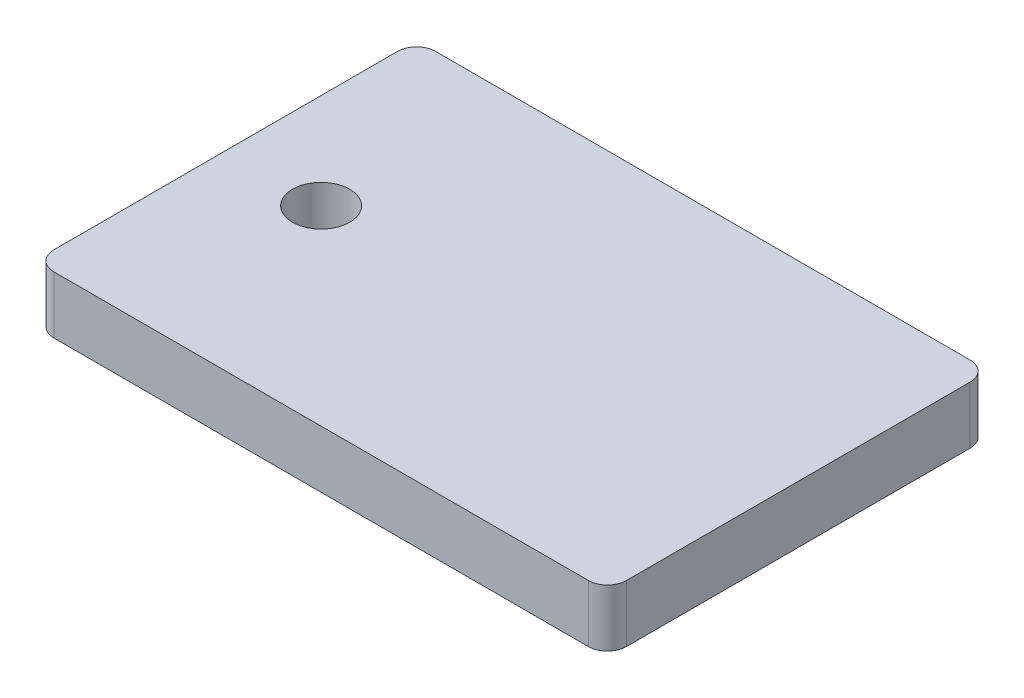
SolidWorks part; units mm, degrees
ref_plane "Front Plane" through (0, 0, 0) normal (0, 0, 1) x (1, 0, 0)
ref_plane "Top Plane" through (0, 0, 0) normal (0, 1, 0) x (1, 0, 0)
ref_plane "Right Plane" through (0, 0, 0) normal (1, 0, 0) x (0, 0, -1)
sketch "Sketch1" plane through (0, 0, 0) normal (0, 1, 0) x (1, 0, 0)
  line L1 (0, 0) -> (30, 0)
  line L2 (0, 0) -> (0, 20)
  line L3 (0, 20) -> (30, 20)
  line L4 (30, 0) -> (30, 20)
  circle A0 centre (5, 10) radius 1.5
  dimension "D3" = 3
  dimension "D1" = 20
  dimension "D2" = 30
  dimension "D4" = 5
extrude "Boss-Extrude1" add sketch "Sketch1" along normal blind 3
fillet "Fillet1" radius 1 4 edges at (0, 1.5, -20) (30, 1.5, -20) (0, 1.5, 0) (30, 1.5, 0)
